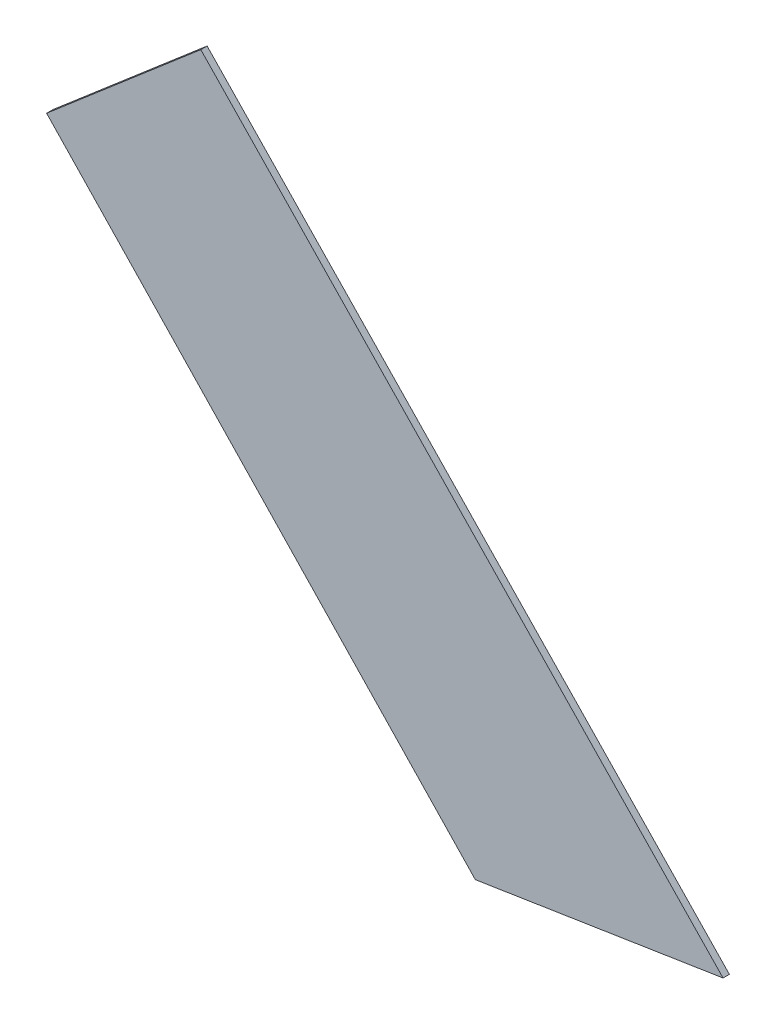
SolidWorks part; units mm, degrees
ref_plane "Alzado" through (0, 0, 0) normal (0, 0, 1) x (1, 0, 0)
ref_plane "Planta" through (0, 0, 0) normal (0, 1, 0) x (1, 0, 0)
ref_plane "Vista lateral" through (0, 0, 0) normal (1, 0, 0) x (0, 0, -1)
sketch "Model" plane through (0, 0, 0) normal (0, 0, 1) x (1, 0, 0)
  line L0 (35.1442, 12.0173) -> (31.2299, 11.4055)
  line L1 (35.1442, 12.0173) -> (26.892, 20.5945)
  line L2 (26.892, 20.5945) -> (24.4558, 18.5063)
  line L3 (24.4558, 18.5063) -> (31.2299, 11.4055)
extrude "Saliente-Extruir1" add sketch "Model" along normal blind 0.1
